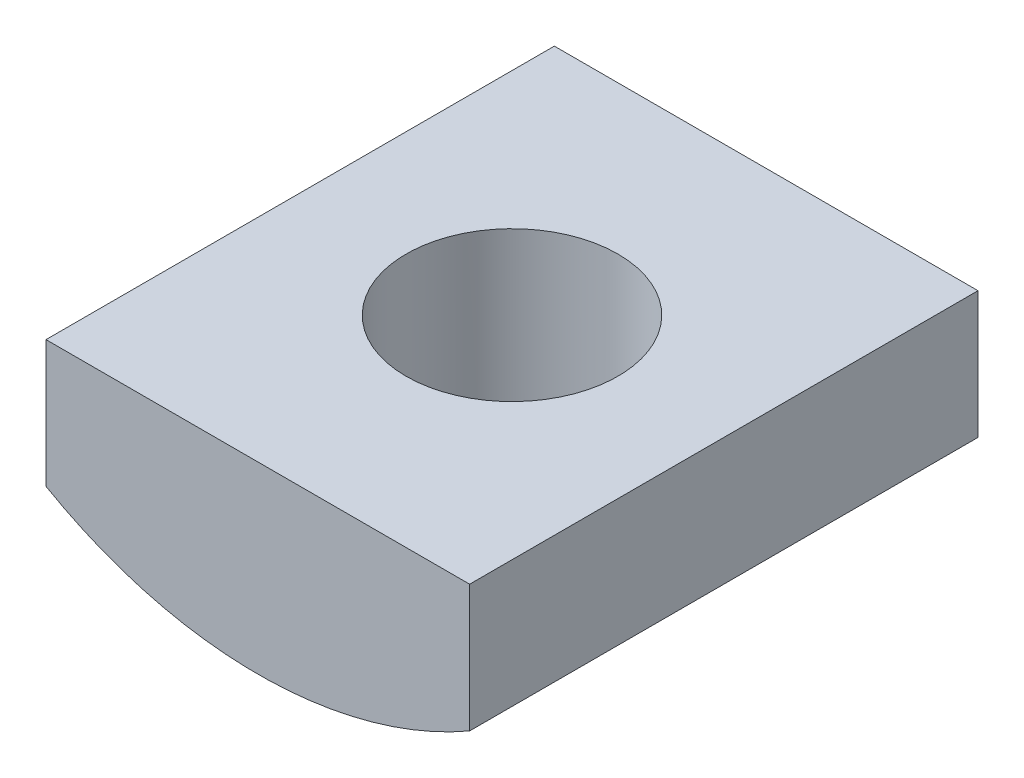
SolidWorks part; units mm, degrees
ref_plane "前基準面" through (0, 0, 0) normal (0, 0, 1) x (1, 0, 0)
ref_plane "上基準面" through (0, 0, 0) normal (0, 1, 0) x (1, 0, 0)
ref_plane "右基準面" through (0, 0, 0) normal (1, 0, 0) x (0, 0, -1)
sketch "草圖1" plane through (0, 0, 0) normal (0, 0, 1) x (1, 0, 0)
  line L1 (-5, 0) -> (5, 0)
  line L2 (-5, 0) -> (-5, -3)
  line L4 (5, 0) -> (5, -3)
  arc A0 (-5, -3) -> (5, -3) centre (0, 5.6603) ccw
  dimension "D3" = 10
  dimension "D1" = 10
  dimension "D2" = 3
extrude "填料-伸長1" add sketch "草圖1" along normal blind 12
hole_wizard "M6x1.0 螺紋孔1" positions "草圖3" profile "草圖2" tap size "M6x1.0" standard "JIS"
sketch "草圖3" plane through (0, 0, 0) normal (0, 1, 0) x (1, 0, 0)
  line L0 (5, -6) -> (-5, -6) construction
  line L1 (5, -12) -> (5, 0) construction
  line L2 (-5, -12) -> (-5, 0) construction
  point P0 (0, -6)
sketch "草圖2" plane through (0, 0, 6) normal (1, 0, 0) x (0, 0, 1)
  line L0 (0, 0) -> (0, 16.5022)
  line L1 (0, 16.5022) -> (2.5, 15)
  line L2 (2.5, 15) -> (2.5, 0)
  line L5 (2.5, 0) -> (0, 0)
  line L10 (0, 16.5022) -> (-2.5, 15) construction
  line L11 (0, -6.35) -> (0, 107.95) construction
  dimension "螺孔鑽直徑" = 5
  dimension "螺孔鑽深度" = 15
  dimension "導頭角度" = 118
